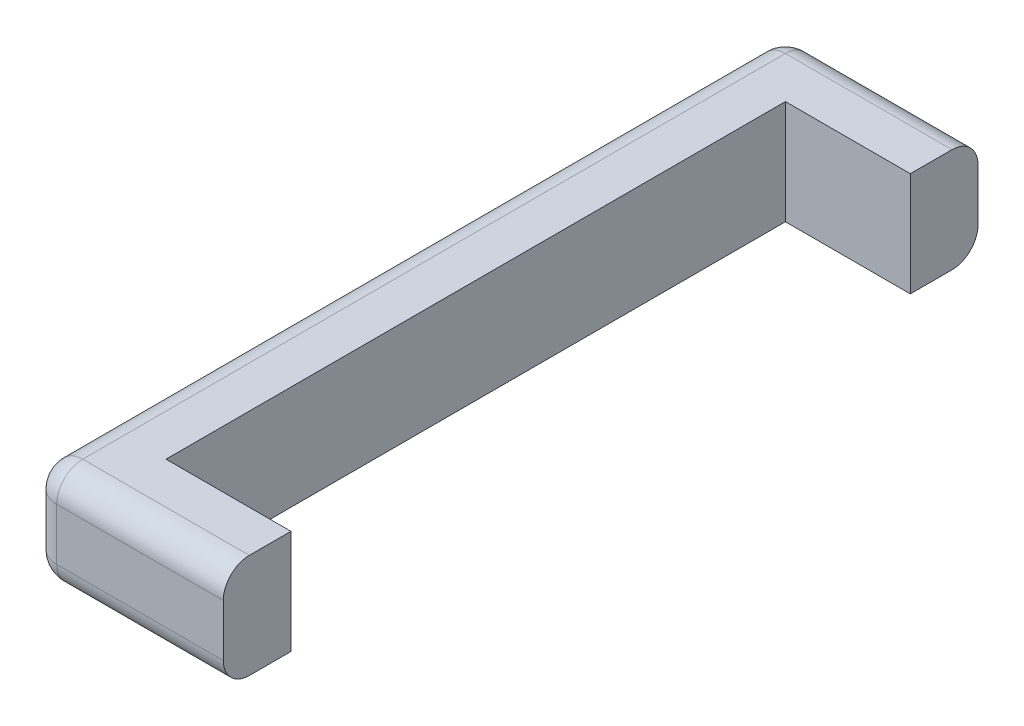
SolidWorks part; units mm, degrees
ref_plane "Front Plane" through (0, 0, 0) normal (0, 0, 1) x (1, 0, 0)
ref_plane "Top Plane" through (0, 0, 0) normal (0, 1, 0) x (1, 0, 0)
ref_plane "Right Plane" through (0, 0, 0) normal (1, 0, 0) x (0, 0, -1)
sketch "Sketch1" plane through (0, 0, 0) normal (0, 1, 0) x (1, 0, 0)
  line L0 (0, 377.825) -> (0, -377.825)
  line L1 (0, -377.825) -> (152.4, -377.825)
  line L2 (152.4, -377.825) -> (152.4, -460.375)
  line L3 (152.4, -460.375) -> (-50.8, -460.375)
  line L4 (-82.55, -428.625) -> (-82.55, 428.625)
  line L5 (-50.8, 460.375) -> (152.4, 460.375)
  line L6 (152.4, 460.375) -> (152.4, 377.825)
  line L7 (152.4, 377.825) -> (0, 377.825)
  arc A0 (-50.8, -460.375) -> (-82.55, -428.625) centre (-50.8, -428.625) cw
  arc A1 (-82.55, 428.625) -> (-50.8, 460.375) centre (-50.8, 428.625) cw
  point P4 (0, 0)
  dimension "D4" = 31.75
  dimension "D1" = 755.65
  dimension "D2" = 82.55
  dimension "D3" = 82.55
  dimension "D5" = 152.4
extrude "Boss-Extrude1" add sketch "Sketch1" along normal mid plane 127
fillet "Fillet1" radius 31.75 10 edges at (50.8, -63.5, -460.375) (-73.2506, -63.5, -451.0756) (50.8, -63.5, 460.375) (-73.2506, -63.5, 451.0756) (50.8, 63.5, -460.375) (-73.2506, 63.5, -451.0756) (50.8, 63.5, 460.375) (-73.2506, 63.5, 451.0756) (-82.55, -63.5, 0) (-82.55, 63.5, 0)
